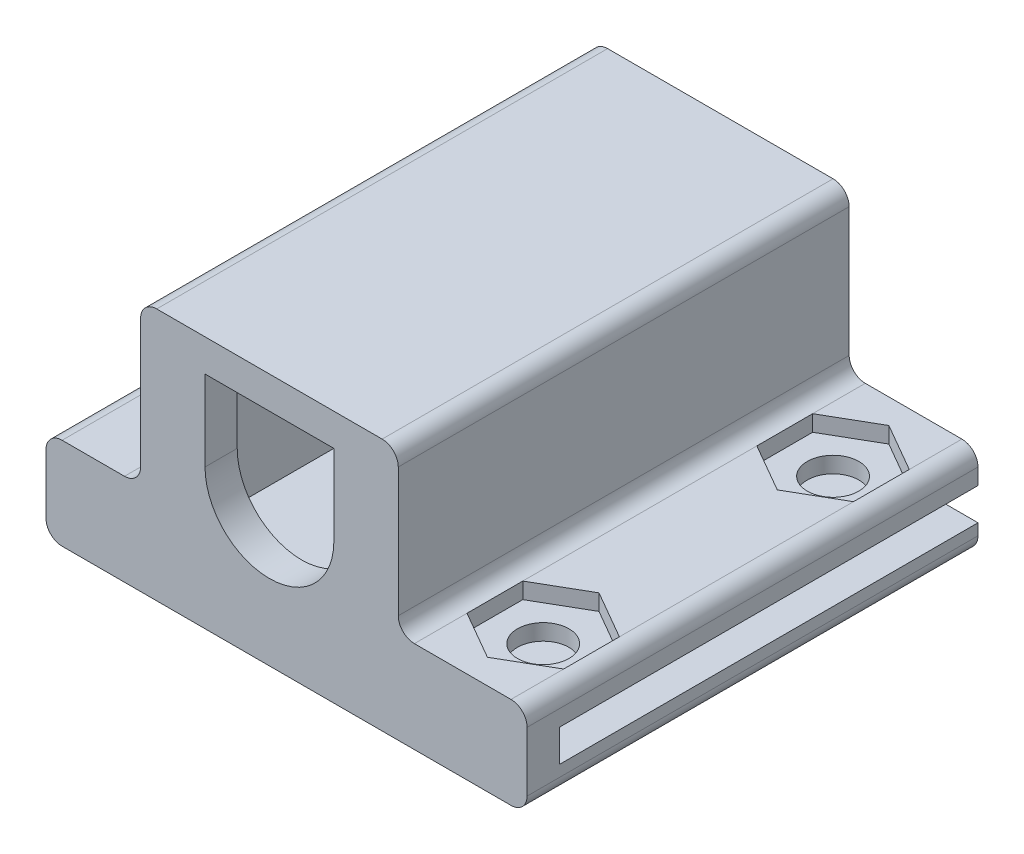
SolidWorks part; units mm, degrees
ref_plane "前视基准面" through (0, 0, 0) normal (0, 0, 1) x (1, 0, 0)
ref_plane "上视基准面" through (0, 0, 0) normal (0, 1, 0) x (1, 0, 0)
ref_plane "右视基准面" through (0, 0, 0) normal (1, 0, 0) x (0, 0, -1)
sketch "草图1" plane through (0, 0, 0) normal (0, 0, 1) x (1, 0, 0)
  line L0 (-5.5, -5) -> (5.5, -5)
  line L1 (-12.875, -3) -> (-9, -3)
  line L2 (-13.875, -4) -> (-13.875, -7.7)
  line L3 (-12.875, -8.7) -> (15, -8.7)
  line L4 (5.5, 5) -> (-5.5, 5)
  line L5 (-6, 4.5) -> (-6, -4.5)
  line L6 (-5.5, -5) -> (5.5, -5)
  line L7 (6, -4.5) -> (6, 4.5)
  line L8 (5.5, 5) -> (-5.5, 5)
  line L9 (-6, 4.5) -> (-6, -4.5)
  line L11 (6, -4.5) -> (6, 4.5)
  line L12 (-11.875, -7) -> (88.125, -7)
  line L13 (88.125, -7) -> (88.125, -5)
  line L14 (88.125, -5) -> (-11.875, -5)
  line L15 (-11.875, -5) -> (-11.875, -7)
  line L17 (88.125, -7) -> (88.125, -5)
  line L20 (16, -4) -> (16, -7.7)
  line L21 (-7, 7) -> (7, 7)
  line L22 (-8, 6) -> (-8, -2)
  line L24 (8, 6) -> (8, -2)
  line L25 (9, -3) -> (15, -3)
  line L27 (0.8292, -1.25) -> (0.8292, 1.25)
  line L28 (0.8292, -1.25) -> (0.8292, 1.25)
  line L30 (-4, 0) -> (-4, 5)
  line L31 (-4, 5) -> (4, 5)
  line L32 (4, 0) -> (4, 5)
  line L35 (88.125, -7) -> (88.125, -5)
  line L37 (-11.875, -5) -> (16, -5)
  line L38 (-11.875, -5) -> (-11.875, -6.7)
  line L39 (-11.875, -6.7) -> (16, -6.7)
  line L40 (16, -5) -> (16, -6.7)
  arc A0 (-4, 0) -> (4, 0) centre (0, 0) ccw
  arc A1 (0.8292, 1.25) -> (0.8292, -1.25) centre (0, 0) ccw
  arc A2 (0.8292, 1.25) -> (0.8292, -1.25) centre (0, 0) ccw
  arc A3 (-7, 7) -> (-8, 6) centre (-7, 6) ccw
  arc A4 (6, 4.5) -> (5.5, 5) centre (5.5, 4.5) ccw
  arc A5 (-5.5, 5) -> (-6, 4.5) centre (-5.5, 4.5) ccw
  arc A6 (-6, -4.5) -> (-5.5, -5) centre (-5.5, -4.5) ccw
  arc A7 (5.5, -5) -> (6, -4.5) centre (5.5, -4.5) ccw
  arc A8 (6, 4.5) -> (5.5, 5) centre (5.5, 4.5) ccw
  arc A9 (-5.5, 5) -> (-6, 4.5) centre (-5.5, 4.5) ccw
  arc A10 (-6, -4.5) -> (-5.5, -5) centre (-5.5, -4.5) ccw
  arc A11 (5.5, -5) -> (6, -4.5) centre (5.5, -4.5) ccw
  arc A12 (-9, -3) -> (-8, -2) centre (-9, -2) ccw
  arc A13 (-12.875, -3) -> (-13.875, -4) centre (-12.875, -4) ccw
  arc A14 (-12.875, -8.7) -> (-13.875, -7.7) centre (-12.875, -7.7) cw
  arc A15 (15, -8.7) -> (16, -7.7) centre (15, -7.7) ccw
  arc A16 (16, -4) -> (15, -3) centre (15, -4) ccw
  arc A17 (8, -2) -> (9, -3) centre (9, -2) ccw
  arc A18 (8, 6) -> (7, 7) centre (7, 6) ccw
  dimension "D11" = 8
  dimension "D12" = 1
  dimension "D3" = 2
  dimension "D4" = 2
  dimension "D5" = 1.7
  dimension "D6" = 2
  dimension "D7" = 2
  dimension "D8" = 8
  dimension "D9" = 2
  dimension "D13" = 2
  dimension "D14" = 2
  dimension "D15" = 10
  dimension "D1" = 0
  dimension "D2" = 0
  dimension "D10" = 0
extrude "凸台-拉伸1" add sketch "草图1" along normal blind 2
sketch "草图2" plane through (0, 0, 0) normal (0, 0, -1) x (-1, 0, 0)
  line L0 (-88.125, -5) -> (11.875, -5) construction
  line L1 (-6, 5) -> (6, 5)
  line L2 (-6, 5) -> (-6, -5)
  line L4 (-6, 4.5) -> (-6, -4.5)
  line L5 (-5.5, -5) -> (5.5, -5)
  line L6 (6, -4.5) -> (6, 4.5)
  line L7 (5.5, 5) -> (-5.5, 5)
  line L8 (-16, -4) -> (-16, -7.7)
  line L9 (-15, -8.7) -> (12.875, -8.7)
  line L10 (13.875, -7.7) -> (13.875, -4)
  line L11 (12.875, -3) -> (9, -3)
  line L12 (8, -2) -> (8, 6)
  line L13 (7, 7) -> (-7, 7)
  line L14 (-8, 6) -> (-8, -2)
  line L15 (-9, -3) -> (-15, -3)
  line L16 (-16, -4) -> (-16, -7.7)
  line L17 (-15, -8.7) -> (12.875, -8.7)
  line L18 (13.875, -7.7) -> (13.875, -4)
  line L19 (12.875, -3) -> (9, -3)
  line L20 (8, -2) -> (8, 6)
  line L21 (7, 7) -> (-7, 7)
  line L22 (-8, 6) -> (-8, -2)
  line L23 (-9, -3) -> (-15, -3)
  line L24 (-6, 4.5) -> (-6, -4.5)
  line L26 (6, -4.5) -> (6, 4.5)
  line L27 (5.5, 5) -> (-5.5, 5)
  line L28 (6, 5) -> (6, -5)
  line L33 (-6, -5) -> (-88.125, -5)
  line L37 (-88.125, -7) -> (11.875, -7)
  line L38 (-88.125, -5) -> (-88.125, -7)
  line L39 (11.875, -5) -> (-88.125, -5)
  line L40 (11.875, -7) -> (11.875, -5)
  line L41 (-88.125, -7) -> (11.875, -7)
  line L42 (-88.125, -5) -> (-88.125, -7)
  line L43 (11.875, -5) -> (6, -5)
  line L44 (11.875, -7) -> (11.875, -5)
  arc A4 (-5.5, 5) -> (-6, 4.5) centre (-5.5, 4.5) ccw
  arc A5 (-6, -4.5) -> (-5.5, -5) centre (-5.5, -4.5) ccw
  arc A6 (5.5, -5) -> (6, -4.5) centre (5.5, -4.5) ccw
  arc A7 (6, 4.5) -> (5.5, 5) centre (5.5, 4.5) ccw
  arc A8 (-5.5, 5) -> (-6, 4.5) centre (-5.5, 4.5) ccw
  arc A11 (6, 4.5) -> (5.5, 5) centre (5.5, 4.5) ccw
  arc A16 (-16, -7.7) -> (-15, -8.7) centre (-15, -7.7) ccw
  arc A17 (-16, -7.7) -> (-15, -8.7) centre (-15, -7.7) ccw
  arc A18 (12.875, -8.7) -> (13.875, -7.7) centre (12.875, -7.7) ccw
  arc A19 (12.875, -8.7) -> (13.875, -7.7) centre (12.875, -7.7) ccw
  arc A20 (13.875, -4) -> (12.875, -3) centre (12.875, -4) ccw
  arc A21 (13.875, -4) -> (12.875, -3) centre (12.875, -4) ccw
  arc A22 (8, -2) -> (9, -3) centre (9, -2) ccw
  arc A23 (8, -2) -> (9, -3) centre (9, -2) ccw
  arc A24 (8, 6) -> (7, 7) centre (7, 6) ccw
  arc A25 (8, 6) -> (7, 7) centre (7, 6) ccw
  arc A26 (-7, 7) -> (-8, 6) centre (-7, 6) ccw
  arc A27 (-7, 7) -> (-8, 6) centre (-7, 6) ccw
  arc A28 (-9, -3) -> (-8, -2) centre (-9, -2) ccw
  arc A29 (-9, -3) -> (-8, -2) centre (-9, -2) ccw
  arc A30 (-15, -3) -> (-16, -4) centre (-15, -4) ccw
  arc A31 (-15, -3) -> (-16, -4) centre (-15, -4) ccw
  point P26 (6, 0)
  line M20 (-16, -4) -> (-16, -7.7)
  line M21 (-15, -8.7) -> (12.875, -8.7)
  line M22 (13.875, -7.7) -> (13.875, -4)
  line M23 (12.875, -3) -> (9, -3)
  line M24 (8, -2) -> (8, 6)
  line M25 (7, 7) -> (-7, 7)
  line M26 (-8, 6) -> (-8, -2)
  line M27 (-9, -3) -> (-15, -3)
  line M28 (-4, 5) -> (4, 5)
  dimension "D3" = 0
  dimension "D4" = 0
  dimension "D5" = 0
  dimension "D1" = 0
  dimension "D2" = 0
extrude "凸台-拉伸2" add sketch "草图2" along normal blind 26 contours L44 L41 L16 L43 L2 L1 L28 L26 M21 M22 M23 M24 M25 M26 M27 M20 M28
sketch "草图5" plane through (0, -3, 0) normal (0, 1, 0) x (1, 0, 0)
  line L0 (12, -2) -> (12, 26) construction
  line L4 (15, -2) -> (15, 26)
  line L5 (15, 26) -> (9, 26)
  line L6 (15, -2) -> (15, 26)
  line L7 (9, -2) -> (15, -2)
  line L11 (9, -2) -> (15, -2)
  line L16 (15, 22.7321) -> (12, 24.4641)
  line L17 (12, 24.4641) -> (9, 22.7321)
  line L19 (9, 26) -> (9, -2)
  line L20 (9, 26) -> (9, -2)
  line L21 (9, 22.7321) -> (9, 19.2679)
  line L22 (9, 19.2679) -> (12, 17.5359)
  line L23 (12, 17.5359) -> (15, 19.2679)
  line L24 (15, 19.2679) -> (15, 22.7321)
  line L28 (15, 26) -> (9, 26)
  circle A1 centre (12, 21) radius 3 construction
  dimension "D3" = 0
  dimension "D4" = 5
  dimension "D2" = 6
  dimension "D1" = 0
extrude "切除-拉伸2" cut sketch "草图5" against normal blind 1 and the other way through all contours L21 L22 L23 L24 L16 L17
sketch "草图6" plane through (0, -3, 0) normal (0, 1, 0) x (1, 0, 0)
  line L0 (12, -2) -> (12, 27) construction
  line L4 (15, 19.2679) -> (12, 17.5359)
  line L5 (12, 17.5359) -> (9, 19.2679)
  line L6 (15, 19.2679) -> (12, 17.5359)
  line L7 (9, -2) -> (15, -2)
  line L11 (9, -2) -> (15, -2)
  line L14 (12, 24.4641) -> (9, 22.7321)
  line L15 (12, 24.4641) -> (9, 22.7321)
  line L16 (9, 22.7321) -> (9, 19.2679)
  line L17 (9, 19.2679) -> (12, 17.5359)
  line L18 (12, 17.5359) -> (15, 19.2679)
  line L19 (15, 19.2679) -> (15, 22.7321)
  line L22 (9, 22.7321) -> (9, 19.2679)
  line L23 (9, 19.2679) -> (12, 17.5359)
  line L24 (12, 17.5359) -> (15, 19.2679)
  line L29 (15, 4.7321) -> (12, 6.4641)
  line L30 (12, 6.4641) -> (9, 4.7321)
  line L32 (9, 4.7321) -> (9, 1.2679)
  line L33 (12, 17.5359) -> (9, 19.2679)
  line L34 (9, 1.2679) -> (12, -0.4641)
  line L35 (15, 19.2679) -> (15, 22.7321)
  line L36 (15, 22.7321) -> (12, 24.4641)
  line L37 (15, 22.7321) -> (12, 24.4641)
  line L38 (9, 19.2679) -> (9, -2)
  line L39 (9, 19.2679) -> (9, -2)
  line L40 (15, -2) -> (15, 19.2679)
  line L41 (15, -2) -> (15, 19.2679)
  line L42 (12, -0.4641) -> (15, 1.2679)
  line L43 (15, 1.2679) -> (15, 4.7321)
  circle A0 centre (12, 3) radius 3 construction
  dimension "D3" = 6
  dimension "D4" = 5
  dimension "D1" = 0
  dimension "D2" = 0
extrude "切除-拉伸3" cut sketch "草图6" against normal blind 1 and the other way through all contours L32 L34 L42 L43 L29 L30
sketch "草图9" plane through (0, -4, 0) normal (0, 1, 0) x (1, 0, 0)
  line L0 (9, 4.7321) -> (15, 1.2679) construction
  line L1 (9, 22.7321) -> (15, 19.2679) construction
  line L6 (12, 6.4641) -> (9, 4.7321)
  line L7 (9, 4.7321) -> (9, 1.2679)
  line L8 (9, 1.2679) -> (12, -0.4641)
  line L9 (12, -0.4641) -> (15, 1.2679)
  line L10 (15, 1.2679) -> (15, 4.7321)
  line L11 (15, 4.7321) -> (12, 6.4641)
  line L12 (12, 6.4641) -> (9, 4.7321)
  line L13 (9, 4.7321) -> (9, 1.2679)
  line L14 (9, 1.2679) -> (12, -0.4641)
  line L15 (12, -0.4641) -> (15, 1.2679)
  line L16 (15, 1.2679) -> (15, 4.7321)
  line L17 (15, 4.7321) -> (12, 6.4641)
  line L18 (12, 24.4641) -> (9, 22.7321)
  line L19 (9, 22.7321) -> (9, 19.2679)
  line L20 (9, 19.2679) -> (12, 17.5359)
  line L21 (12, 17.5359) -> (15, 19.2679)
  line L22 (15, 19.2679) -> (15, 22.7321)
  line L23 (15, 22.7321) -> (12, 24.4641)
  line L24 (12, 24.4641) -> (9, 22.7321)
  line L25 (9, 22.7321) -> (9, 19.2679)
  line L26 (9, 19.2679) -> (12, 17.5359)
  line L27 (12, 17.5359) -> (15, 19.2679)
  line L28 (15, 19.2679) -> (15, 22.7321)
  line L29 (15, 22.7321) -> (12, 24.4641)
  circle A0 centre (12, 3) radius 1.6
  circle A1 centre (12, 21) radius 1.6
  dimension "D3" = 3.2
  dimension "D4" = 3.2
  dimension "D1" = 0
  dimension "D2" = 0
extrude "切除-拉伸4" cut sketch "草图9" against normal through all contours A0 | A1
sketch "草图10" plane through (0, 0, -26) normal (0, 0, -1) x (-1, 0, 0)
  line L1 (-6, 5) -> (6, 5)
  line L2 (-6, 5) -> (-6, 4)
  line L3 (-6, 4) -> (6, 4)
  line L4 (6, 5) -> (6, 4)
  line L16 (11.875, -5) -> (11.875, -7)
  line L17 (11.875, -7) -> (-16, -7)
  line L18 (-16, -7) -> (-16, -7.7)
  line L19 (-15, -8.7) -> (12.875, -8.7)
  line L20 (13.875, -7.7) -> (13.875, -4)
  line L21 (12.875, -3) -> (9, -3)
  line L22 (8, -2) -> (8, 6)
  line L23 (7, 7) -> (-7, 7)
  line L24 (-8, 6) -> (-8, -2)
  line L25 (-9, -3) -> (-15, -3)
  line L26 (-16, -4) -> (-16, -5)
  line L27 (-16, -5) -> (-6, -5)
  line L28 (-6, -5) -> (-6, 5)
  line L29 (-6, 5) -> (6, 5)
  line L30 (6, 5) -> (6, -5)
  line L31 (6, -5) -> (11.875, -5)
  line L32 (11.875, -5) -> (11.875, -7)
  line L33 (11.875, -7) -> (-16, -7)
  line L34 (-16, -7) -> (-16, -7.7)
  line L35 (-15, -8.7) -> (12.875, -8.7)
  line L36 (13.875, -7.7) -> (13.875, -4)
  line L37 (12.875, -3) -> (9, -3)
  line L38 (8, -2) -> (8, 6)
  line L39 (7, 7) -> (-7, 7)
  line L40 (-8, 6) -> (-8, -2)
  line L41 (-9, -3) -> (-15, -3)
  line L42 (-16, -4) -> (-16, -5)
  line L43 (-16, -5) -> (-6, -5)
  line L44 (-6, -5) -> (-6, 5)
  line L45 (-6, 5) -> (6, 5)
  line L46 (6, 5) -> (6, -5)
  line L47 (6, -5) -> (11.875, -5)
  arc A8 (-16, -7.7) -> (-15, -8.7) centre (-15, -7.7) ccw
  arc A9 (12.875, -8.7) -> (13.875, -7.7) centre (12.875, -7.7) ccw
  arc A10 (13.875, -4) -> (12.875, -3) centre (12.875, -4) ccw
  arc A11 (8, -2) -> (9, -3) centre (9, -2) ccw
  arc A12 (8, 6) -> (7, 7) centre (7, 6) ccw
  arc A13 (-7, 7) -> (-8, 6) centre (-7, 6) ccw
  arc A14 (-9, -3) -> (-8, -2) centre (-9, -2) ccw
  arc A15 (-15, -3) -> (-16, -4) centre (-15, -4) ccw
  arc A16 (-16, -7.7) -> (-15, -8.7) centre (-15, -7.7) ccw
  arc A17 (12.875, -8.7) -> (13.875, -7.7) centre (12.875, -7.7) ccw
  arc A18 (13.875, -4) -> (12.875, -3) centre (12.875, -4) ccw
  arc A19 (8, -2) -> (9, -3) centre (9, -2) ccw
  arc A20 (8, 6) -> (7, 7) centre (7, 6) ccw
  arc A21 (-7, 7) -> (-8, 6) centre (-7, 6) ccw
  arc A22 (-9, -3) -> (-8, -2) centre (-9, -2) ccw
  arc A23 (-15, -3) -> (-16, -4) centre (-15, -4) ccw
  line M47 (-6, -5) -> (-6, 5)
  line M48 (-6, 5) -> (6, 5)
  line M49 (6, 5) -> (6, -5)
  dimension "D2" = 1
  dimension "D1" = 0
extrude "凸台-拉伸3" add sketch "草图10" against normal blind 1.6 separate body contours L3 M47 M49 M48
